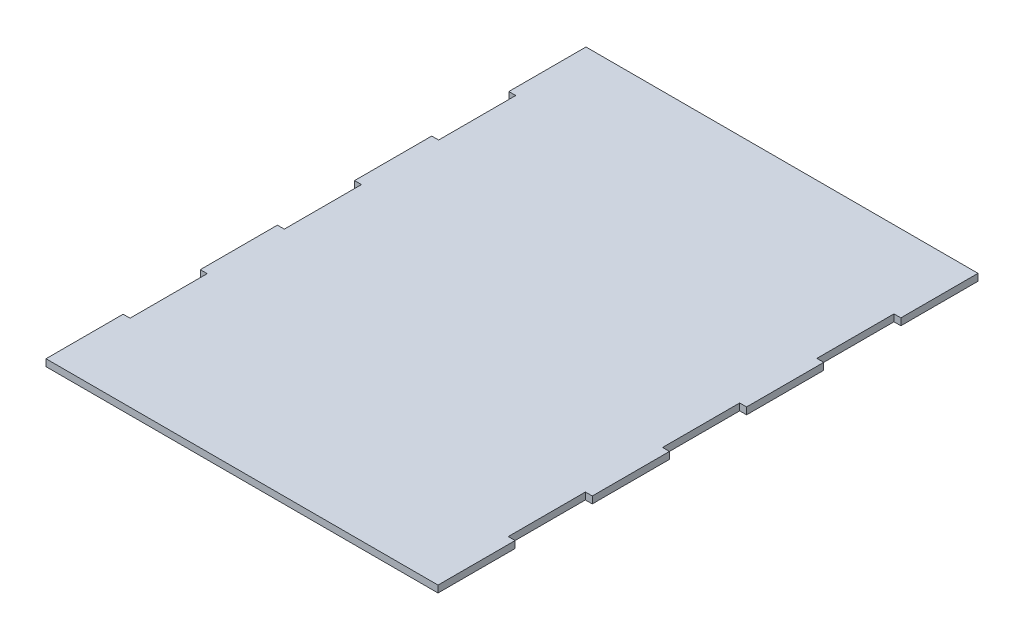
SolidWorks part; units mm, degrees
ref_plane "Ön Düzlem" through (0, 0, 0) normal (0, 0, 1) x (1, 0, 0)
ref_plane "Üst Düzlem" through (0, 0, 0) normal (0, 1, 0) x (1, 0, 0)
ref_plane "Sağ Düzlem" through (0, 0, 0) normal (1, 0, 0) x (0, 0, -1)
sketch "Sketch1" plane through (0, 0, 0) normal (0, 1, 0) x (1, 0, 0)
  line L1 (76.7, -105.6474) -> (-76.7, -105.6474)
  line L4 (-76.7, -105.6474) -> (-76.7, -75.4624)
  line L5 (76.7, 105.6474) -> (-76.7, 105.6474)
  line L6 (-74, 75.4624) -> (-74, 45.2774)
  line L7 (-76.7, -45.2774) -> (-76.7, -15.0925)
  line L9 (-76.7, 15.0925) -> (-76.7, 45.2774)
  line L11 (-76.7, 75.4624) -> (-76.7, 105.6474)
  line L12 (-76.7, 75.4624) -> (-74, 75.4624)
  line L13 (-76.7, 45.2774) -> (-74, 45.2774)
  line L14 (-76.7, 15.0925) -> (-74, 15.0925)
  line L15 (-76.7, -15.0925) -> (-74, -15.0925)
  line L16 (-76.7, -45.2774) -> (-74, -45.2774)
  line L17 (-76.7, -75.4624) -> (-74, -75.4624)
  line L18 (74, 15.0925) -> (74, -15.0925)
  line L19 (74, -45.2774) -> (74, -75.4624)
  line L20 (76.7, -75.4624) -> (74, -75.4624)
  line L21 (76.7, -45.2774) -> (74, -45.2774)
  line L22 (76.7, -15.0925) -> (74, -15.0925)
  line L23 (76.7, 15.0925) -> (74, 15.0925)
  line L24 (76.7, 45.2774) -> (74, 45.2774)
  line L25 (76.7, 75.4624) -> (74, 75.4624)
  line L26 (-74, -45.2774) -> (-74, -75.4624)
  line L27 (-74, 15.0925) -> (-74, -15.0925)
  line L29 (76.7, 75.4624) -> (76.7, 105.6474)
  line L30 (76.7, 15.0925) -> (76.7, 45.2774)
  line L31 (76.7, -45.2774) -> (76.7, -15.0925)
  line L32 (74, 75.4624) -> (74, 45.2774)
  line L34 (76.7, -105.6474) -> (76.7, -75.4624)
  point P0 (0, 0)
  dimension "D1" = 211.2947
extrude "Boss-Extrude1" add sketch "Sketch1" along normal blind 2.7
